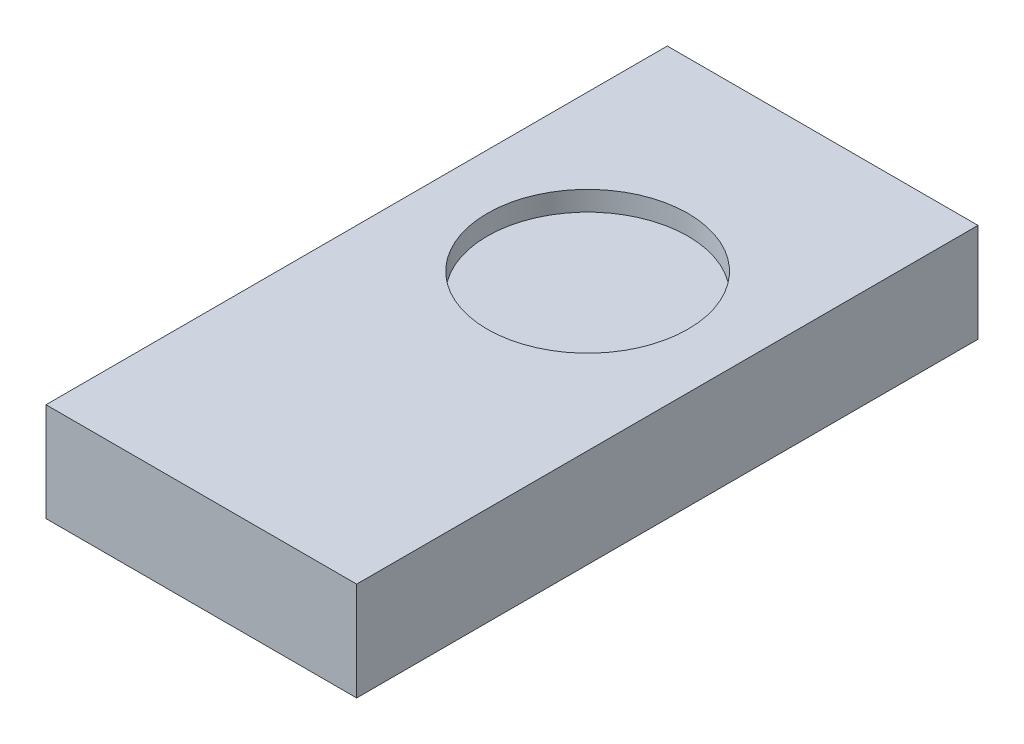
SolidWorks part; units mm, degrees
ref_plane "Front Plane" through (0, 0, 0) normal (0, 0, 1) x (1, 0, 0)
ref_plane "Top Plane" through (0, 0, 0) normal (0, 1, 0) x (1, 0, 0)
ref_plane "Right Plane" through (0, 0, 0) normal (1, 0, 0) x (0, 0, -1)
sketch "Sketch1" plane through (0, 0, 0) normal (0, 1, 0) x (1, 0, 0)
  line L1 (0, 0) -> (10, 0)
  line L2 (0, 0) -> (0, 20)
  line L3 (0, 20) -> (10, 20)
  line L4 (10, 0) -> (10, 20)
  dimension "D1" = 10
  dimension "D2" = 20
extrude "Boss-Extrude1" add sketch "Sketch1" along normal blind 3.175
sketch "Sketch2" plane through (0, 3.175, 0) normal (0, 1, 0) x (1, 0, 0)
  circle A0 centre (4.9965, 12.437) radius 3.2303
extrude "Cut-Extrude1" cut sketch "Sketch2" against normal blind 0.635
